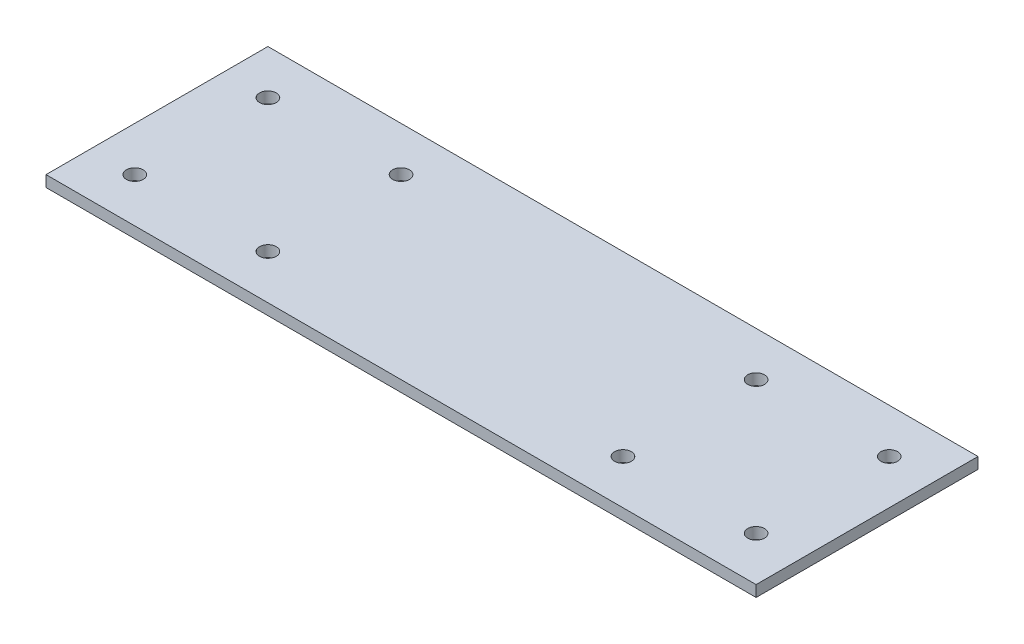
SolidWorks part; units mm, degrees
ref_plane "Front Plane" through (0, 0, 0) normal (0, 0, 1) x (1, 0, 0)
ref_plane "Top Plane" through (0, 0, 0) normal (0, 1, 0) x (1, 0, 0)
ref_plane "Right Plane" through (0, 0, 0) normal (1, 0, 0) x (0, 0, -1)
sketch "Sketch1" plane through (0, 0, 0) normal (0, 1, 0) x (1, 0, 0)
  line L1 (-50.8, -15.875) -> (50.8, -15.875)
  line L2 (-50.8, -15.875) -> (-50.8, 15.875)
  line L3 (-50.8, 15.875) -> (50.8, 15.875)
  line L4 (50.8, -15.875) -> (50.8, 15.875)
  line L5 (-50.8, -15.875) -> (50.8, 15.875) construction
  line L6 (-50.8, 15.875) -> (50.8, -15.875) construction
  point P0 (0, 0)
  dimension "D1" = 31.75
  dimension "D2" = 101.6
extrude "Boss-Extrude1" add sketch "Sketch1" along normal blind 1.6002
sketch "Sketch2" plane through (0, 1.6002, 0) normal (0, 1, 0) x (1, 0, 0)
  line L0 (-1050.8, 0) -> (48949.2, 0) construction
  line L1 (-44.45, -9.525) -> (-25.4, -9.525)
  line L2 (-44.45, -9.525) -> (-44.45, 9.525)
  line L3 (-44.45, 9.525) -> (-25.4, 9.525)
  line L4 (-25.4, -9.525) -> (-25.4, 9.525)
  line L5 (-44.45, -9.525) -> (-25.4, 9.525) construction
  line L6 (-44.45, 9.525) -> (-25.4, -9.525) construction
  line L7 (-50.8, 15.875) -> (-50.8, -15.875) construction
  line L8 (50.8, 15.875) -> (-50.8, 15.875) construction
  point P0 (-34.925, 0)
  point P6 (0, 0)
  point P10 (-50.8, 0)
  dimension "D1" = 19.05
  dimension "D2" = 19.05
  dimension "D3" = 6.35
  dimension "D4" = 6.35
hole_wizard "M2 Clearance Hole1" positions "Sketch3" profile "Sketch4" hole size "M2" standard "ANSI Metric" end condition through all
sketch "Sketch3" plane through (0, 1.6002, 0) normal (0, 1, 0) x (1, 0, 0)
  point P0 (-25.4, 9.525)
  point P3 (-44.45, 9.525)
  point P6 (-44.45, -9.525)
  point P9 (-25.4, -9.525)
sketch "Sketch4" plane through (-25.4, 1.6002, -9.525) normal (1, 0, 0) x (0, 0, 1)
  line L0 (0, 0) -> (0, 1.6002)
  line L1 (0, 1.6002) -> (1.2, 1.6002)
  line L2 (1.2, 1.6002) -> (1.2, 0)
  line L5 (1.2, 0) -> (0, 0)
  line L11 (0, -6.35) -> (0, 107.95) construction
  dimension "Thru Hole Dia." = 2.4
  dimension "Thru Hole Depth" = 1.6002
mirror "Mirror1" about plane through (0, 0, 0) normal (1, 0, 0) of "M2 Clearance Hole1"
equation "\"D2@Sketch2\"=\"D1@Sketch2\""
equation "\"D4@Sketch2\"=\"D3@Sketch2\""
